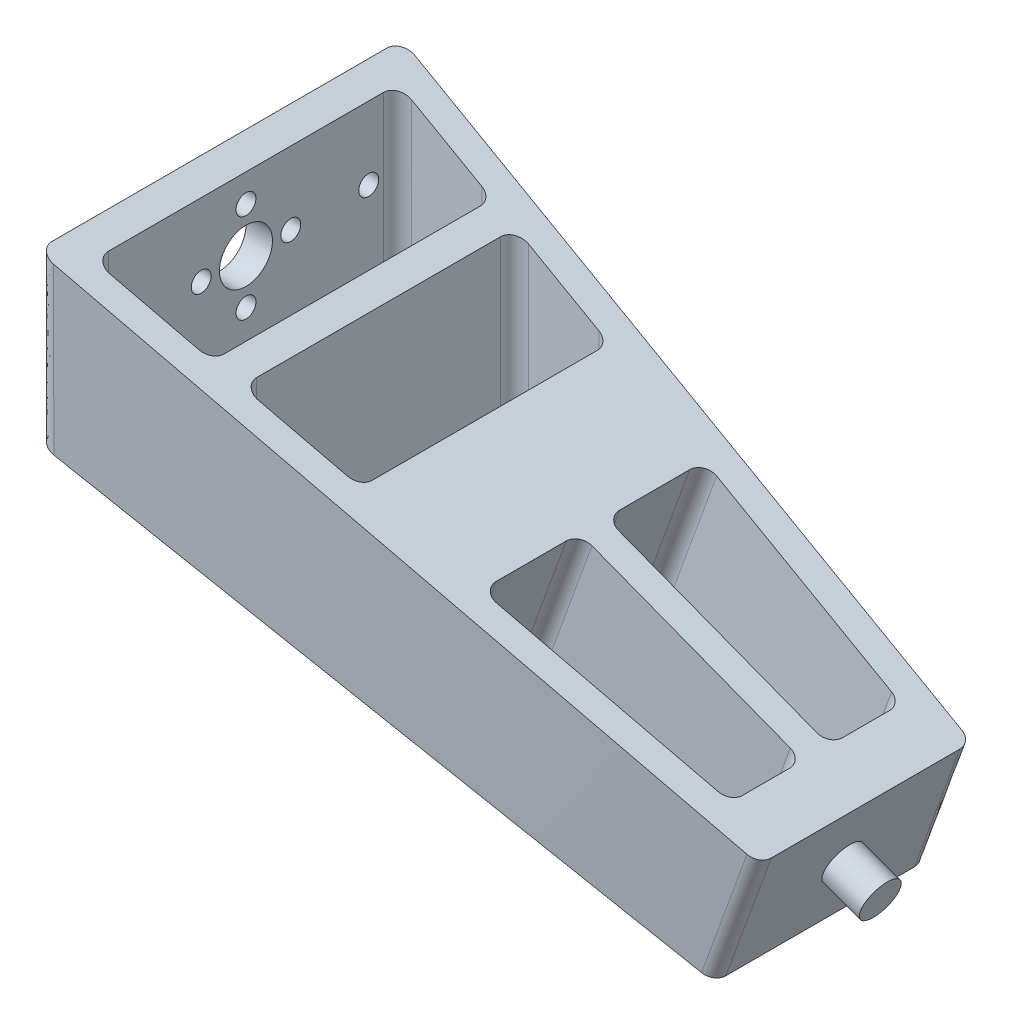
SolidWorks part; units mm, degrees
material "Окись алюминия"
ref_plane "Спереди" through (0, 0, 0) normal (0, 0, 1) x (1, 0, 0)
ref_plane "Сверху" through (0, 0, 0) normal (0, 1, 0) x (1, 0, 0)
ref_plane "Справа" through (0, 0, 0) normal (1, 0, 0) x (0, 0, -1)
other "Configuration Table"
sketch "Эскиз1" plane through (0, 0, 0) normal (0, 0, 1) x (1, 0, 0)
  line L0 (0, 0) -> (93.9693, -34.202) construction
  line L1 (0, 0) -> (29.5424, 0) construction
  line L2 (93.9693, -34.202) -> (110.087, 10.0812) construction
  point P6 (93.9693, -34.202)
  dimension "D1" = 20
  dimension "D2" = 100
sketch "Эскиз2" plane through (0, 0, 0) normal (1, 0, 0) x (0, 0, -1)
  line L0 (-27.5, -12.5) -> (27.5, 12.5) construction
  line L1 (-27.5, 12.5) -> (27.5, 12.5)
  line L2 (-27.5, 12.5) -> (-27.5, -12.5)
  line L3 (-27.5, -12.5) -> (27.5, -12.5)
  line L4 (27.5, 12.5) -> (27.5, -12.5)
  dimension "D1" = 55
  dimension "D2" = 25
ref_plane "Плоскость1" through (93.9693, -34.202, 0) normal (0.9397, -0.342, 0) x (0, 0, -1)
sketch "Эскиз3" plane through (93.9693, -34.202, 0) normal (0.9397, -0.342, 0) x (0, 0, -1)
  line L1 (-16, -10) -> (16, -10)
  line L2 (-16, -10) -> (-16, 10)
  line L3 (-16, 10) -> (16, 10)
  line L4 (16, -10) -> (16, 10)
  line L5 (-16, -10) -> (16, 10) construction
  line L6 (-16, 10) -> (16, -10) construction
  point P0 (0, 0)
  dimension "D1" = 32
  dimension "D2" = 20
loft "По сечениям1" add profiles "Эскиз3", "Эскиз2"
sketch "Эскиз4" plane through (93.9693, -34.202, 0) normal (0.9397, -0.342, 0) x (0, 0, -1)
  circle A0 centre (0, 0) radius 3
  dimension "D1" = 6
extrude "Бобышка-Вытянуть1" add sketch "Эскиз4" along normal blind 6 contours A0
fillet "Скругление1" radius 2 4 edges
sketch "Эскиз5" plane through (0, 0, 0) normal (0, 1, 0) x (1, 0, 0)
  line L8 (4, 22.9999) -> (4, -22.9999) construction
  line L9 (4, -22.9999) -> (40, -18.7489) construction
  line L10 (40, -18.7489) -> (40, 18.7489) construction
  line L11 (40, 18.7489) -> (4, 22.9999) construction
  line L12 (4, 0) -> (40, 0) construction
  line L13 (-68310.0594, 0) -> (68514.1157, 0) construction
  line L14 (0, 25.2506) -> (0, -25.2506) construction
  line L15 (95.7263, -16.1964) -> (2.234, -27.2362) construction
  line L16 (95.7263, 16.1964) -> (2.234, 27.2362) construction
  line L17 (24, 20.6382) -> (24, -20.6382) construction
  line L18 (20, 21.1106) -> (20, -21.1106) construction
  line L19 (18.2345, 21.319) -> (6.2345, 22.736)
  line L20 (4, 20.7498) -> (4, -20.7498)
  line L21 (6.2345, -22.736) -> (18.2345, -21.319)
  line L22 (20, -19.3328) -> (20, 19.3328)
  line L23 (24, 18.3882) -> (24, -18.3882)
  line L24 (26.2345, -20.3744) -> (38.2345, -18.9574)
  line L25 (40, -16.9712) -> (40, 16.9712)
  line L26 (38.2345, 18.9574) -> (26.2345, 20.3744)
  arc A4 (40, 16.9712) -> (38.2345, 18.9574) centre (38, 16.9712) ccw
  arc A5 (38.2345, -18.9574) -> (40, -16.9712) centre (38, -16.9712) ccw
  arc A6 (26.2345, -20.3744) -> (24, -18.3882) centre (26, -18.3882) cw
  arc A7 (26.2345, 20.3744) -> (24, 18.3882) centre (26, 18.3882) ccw
  arc A8 (20, 19.3328) -> (18.2345, 21.319) centre (18, 19.3328) ccw
  arc A9 (20, -19.3328) -> (18.2345, -21.319) centre (18, -19.3328) cw
  arc A10 (4, -20.7498) -> (6.2345, -22.736) centre (6, -20.7498) ccw
  arc A11 (6.2345, 22.736) -> (4, 20.7498) centre (6, 20.7498) ccw
  point P8 (22, 0)
  dimension "D5" = 2
  dimension "D6" = 2
  dimension "D1" = 4
  dimension "D2" = 36
  dimension "D3" = 4
  dimension "D4" = 2
ref_plane "Плоскость2" through (0, 0, 0) normal (0.342, 0.9397, 0) x (0.9397, -0.342, 0)
sketch "Эскиз6" plane through (0, 0, 0) normal (0.342, 0.9397, 0) x (0.9397, -0.342, 0)
  line L7 (56, 14.5956) -> (56, 4)
  line L9 (90.2192, 13.0544) -> (58.2192, 16.5835)
  line L11 (92, 11.0665) -> (92, 4)
  line L12 (100, 14.2085) -> (100, -14.2085) construction
  line L14 (98.2193, 16.1964) -> (-1.8833, 27.2362) construction
  line L15 (58, 2) -> (90, 2)
  line L16 (0, 0) -> (100, 0) construction
  line L17 (0, 0) -> (100, 0) construction
  line L18 (92, -11.0665) -> (92, -4)
  line L19 (90.2192, -13.0544) -> (58.2192, -16.5835)
  line L20 (56, -14.5956) -> (56, -4)
  line L21 (58, -2) -> (90, -2)
  arc A4 (92, 11.0665) -> (90.2192, 13.0544) centre (90, 11.0665) ccw
  arc A5 (90, 2) -> (92, 4) centre (90, 4) ccw
  arc A6 (58, 2) -> (56, 4) centre (58, 4) cw
  arc A7 (58.2192, 16.5835) -> (56, 14.5956) centre (58, 14.5956) ccw
  arc A8 (90, -2) -> (92, -4) centre (90, -4) cw
  arc A9 (92, -11.0665) -> (90.2192, -13.0544) centre (90, -11.0665) cw
  arc A10 (58.2192, -16.5835) -> (56, -14.5956) centre (58, -14.5956) cw
  arc A11 (58, -2) -> (56, -4) centre (58, -4) ccw
  point P16 (92, 2)
  point P19 (56, 2)
  dimension "D4" = 2
  dimension "D5" = 2
  dimension "D1" = 8
  dimension "D2" = 4
  dimension "D3" = 36
sketch "Эскиз7" plane through (0, 0, 0) normal (-1, 0, 0) x (0, 0, 1)
  line L0 (50, 0) -> (-50, 0) construction
  line L1 (0, 6.75) -> (0, 0) construction
  circle A0 centre (0, 0) radius 4
  circle A1 centre (0, 0) radius 6.75 construction
  circle A2 centre (18.5, 0) radius 1.5
  circle A5 centre (0, 0) radius 6.75 construction
  circle A7 centre (0, 0) radius 6.75 construction
  circle A9 centre (0, 0) radius 6.75 construction
  circle A11 centre (0, 0) radius 6.75 construction
  circle A13 centre (0, 0) radius 6.75 construction
  circle A15 centre (0, 0) radius 6.75 construction
  circle A17 centre (0, 0) radius 6.75 construction
  circle A18 centre (-18.5, 0) radius 1.5
  circle A19 centre (0, 6.75) radius 1.5
  circle A20 centre (6.75, 0) radius 1.5
  circle A21 centre (0, 0) radius 6.75 construction
  circle A22 centre (0, -6.75) radius 1.5
  circle A23 centre (0, 0) radius 6.75 construction
  circle A24 centre (-6.75, 0) radius 1.5
  circle A25 centre (0, 0) radius 6.75 construction
  point P4 (18.5, 0)
  point P9 (0, 6.75)
  point P15 (4.773, 4.773)
  point P19 (6.75, 0)
  point P23 (4.773, -4.773)
  point P27 (0, -6.75)
  point P31 (-4.773, -4.773)
  point P35 (-6.75, 0)
  point P39 (-4.773, 4.773)
  point P40 (0, 0)
  point P42 (0, 0)
  dimension "D1" = 8
  dimension "D2" = 13.5
  dimension "D4" = 3
  dimension "D3" = 18.5
  dimension "D6" = 8
extrude "Вырез-Вытянуть5" cut sketch "Эскиз5" against normal through all both and the other way through all
extrude "Вырез-Вытянуть4" cut sketch "Эскиз6" against normal through all both and the other way through all
extrude "Вырез-Вытянуть6" cut sketch "Эскиз7" against normal up to surface (4 mm away) up to face at (4, -1.453, 0)
